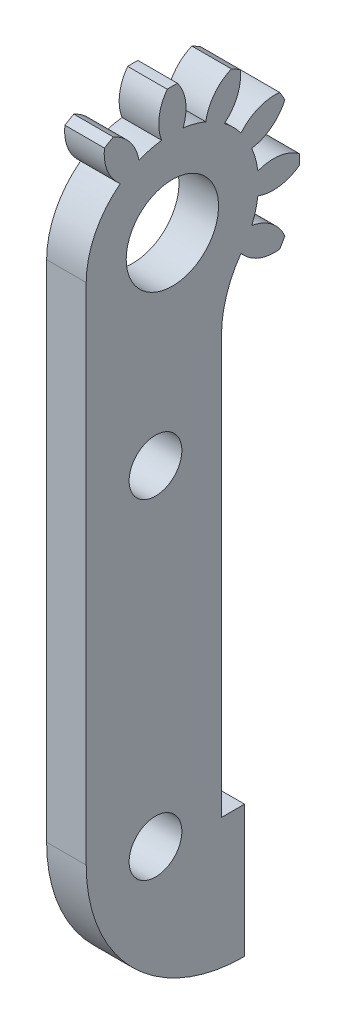
SolidWorks part; units mm, degrees
material "Balsa"
ref_plane "Alzado" through (0, 0, 0) normal (0, 0, 1) x (1, 0, 0)
ref_plane "Planta" through (0, 0, 0) normal (0, 1, 0) x (1, 0, 0)
ref_plane "Vista lateral" through (0, 0, 0) normal (1, 0, 0) x (0, 0, -1)
ref_plane "Plano1" through (2.8161, 0, 0) normal (1, 0, 0) x (0, 0, -1)
sketch "Croquis1" plane through (2.8161, 0, 0) normal (1, 0, 0) x (0, 0, -1)
  line L0 (-6.3041, 0.2301) -> (-6.3041, -38)
  line L1 (5.6959, -50) -> (5.6959, -40)
  line L2 (5.6959, -40) -> (3.9459, -40)
  line L3 (3.9459, -40) -> (3.9459, -8.3564)
  circle A0 centre (-1.0541, -14.4108) radius 2
  circle A1 centre (-1.0541, -39.4108) radius 2
  circle A2 centre (0.2262, 0.2301) radius 3.5
  arc A3 (-3.72, 5.4332) -> (-6.3041, 0.2301) centre (0.2262, 0.2301) ccw
  arc A4 (-6.3041, -38) -> (5.6959, -50) centre (5.6959, -38) ccw
  arc A5 (3.9459, -8.3564) -> (5.4293, -3.716) centre (11.9459, -8.3564) cw
  arc A6 (5.4293, -3.716) -> (8.3596, -4.9166) centre (7.9921, -1.6371) ccw
  arc A7 (8.3596, -4.9166) -> (8.7501, -4.2402) centre (0.2262, 0.2301) ccw
  arc A8 (8.7501, -4.2402) -> (6.2452, -2.3028) centre (5.7262, -5.5617) ccw
  arc A9 (6.2452, -2.3028) -> (6.7053, -0.5858) centre (0.2262, 0.2301) ccw
  arc A10 (6.7053, -0.5858) -> (9.8433, -0.1604) centre (7.8853, 2.496) ccw
  arc A11 (9.8433, -0.1604) -> (9.8433, 0.6206) centre (0.2262, 0.2301) ccw
  arc A12 (9.8433, 0.6206) -> (6.7053, 1.0461) centre (7.8853, -2.0358) ccw
  arc A13 (6.7053, 1.0461) -> (6.2452, 2.763) centre (0.2262, 0.2301) ccw
  arc A14 (6.2452, 2.763) -> (8.7501, 4.7005) centre (5.7262, 6.022) ccw
  arc A15 (8.7501, 4.7005) -> (8.3596, 5.3768) centre (0.2262, 0.2301) ccw
  arc A16 (8.3596, 5.3768) -> (5.4293, 4.1763) centre (7.9921, 2.0974) ccw
  arc A17 (5.4293, 4.1763) -> (4.1724, 5.4332) centre (0.2262, 0.2301) ccw
  arc A18 (4.1724, 5.4332) -> (5.3729, 8.3635) centre (2.0934, 7.996) ccw
  arc A19 (5.3729, 8.3635) -> (4.6966, 8.754) centre (0.2262, 0.2301) ccw
  arc A20 (4.6966, 8.754) -> (2.7591, 6.2491) centre (6.018, 5.7301) ccw
  arc A21 (2.7591, 6.2491) -> (1.0421, 6.7092) centre (0.2262, 0.2301) ccw
  arc A22 (1.0421, 6.7092) -> (0.6167, 9.8472) centre (-2.0397, 7.8892) ccw
  arc A23 (0.6167, 9.8472) -> (-0.1643, 9.8472) centre (0.2262, 0.2301) ccw
  arc A24 (-0.1643, 9.8472) -> (-0.5897, 6.7092) centre (2.4921, 7.8892) ccw
  arc A25 (-0.5897, 6.7092) -> (-2.3067, 6.2491) centre (0.2262, 0.2301) ccw
  arc A26 (-2.3067, 6.2491) -> (-4.2442, 8.754) centre (-5.5656, 5.7301) ccw
  arc A27 (-4.2442, 8.754) -> (-4.9205, 8.3635) centre (0.2262, 0.2301) ccw
  arc A28 (-4.9205, 8.3635) -> (-3.72, 5.4332) centre (-1.641, 7.996) ccw
  dimension "D1" = 4
  dimension "D3" = 4
  dimension "D2" = 38.2301
extrude "Saliente-Extruir1" add sketch "Croquis1" against normal blind 3
